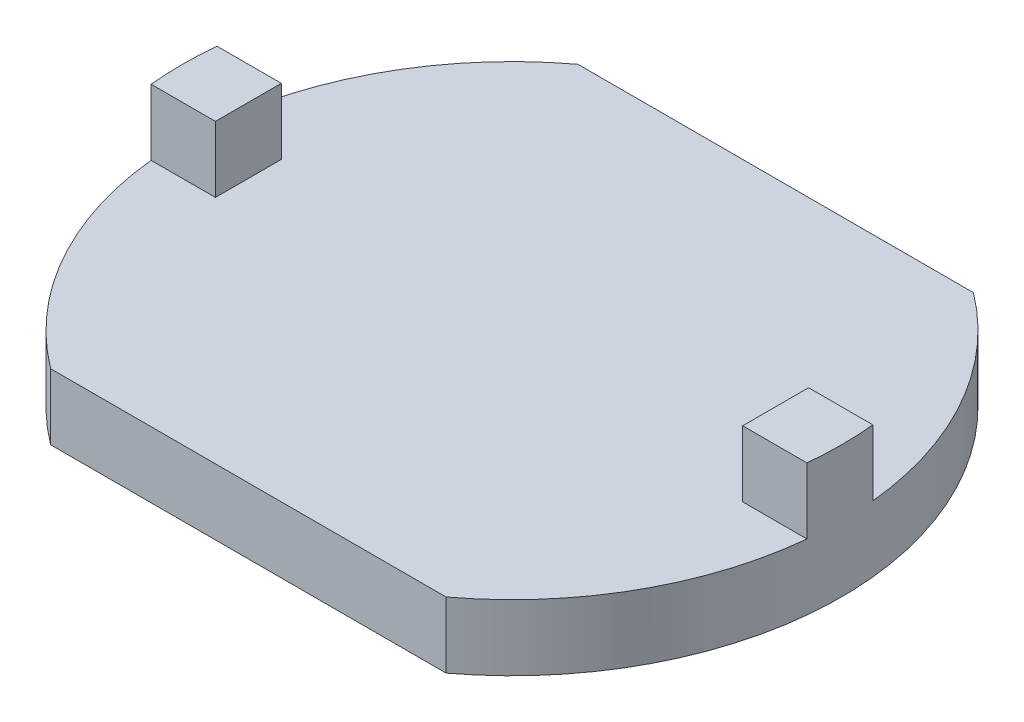
SolidWorks part; units mm, degrees
ref_plane "Front Plane" through (0, 0, 0) normal (0, 0, 1) x (1, 0, 0)
ref_plane "Top Plane" through (0, 0, 0) normal (0, 1, 0) x (1, 0, 0)
ref_plane "Right Plane" through (0, 0, 0) normal (1, 0, 0) x (0, 0, -1)
sketch "Sketch1" plane through (0, 0, 0) normal (0, 1, 0) x (1, 0, 0)
  line L0 (-3, 4) -> (3, 4)
  line L1 (-2.1272, 0) -> (4.3012, 0) construction
  line L2 (-3, -4) -> (3, -4)
  arc A0 (-3, 4) -> (-3, -4) centre (0, 0) ccw
  arc A1 (3, -4) -> (3, 4) centre (0, 0) ccw
  dimension "D1" = 10
  dimension "D2" = 4
extrude "Boss-Extrude1" add sketch "Sketch1" along normal blind 1 contours A0 L2 A1 L0
sketch "Sketch2" plane through (0, 1, 0) normal (0, 1, 0) x (1, 0, 0)
  line L0 (-1.3705, 0) -> (4.9727, 0) construction
  line L1 (0, 1.7654) -> (0, -2.0379) construction
  line L2 (4, -0.5) -> (4.9749, -0.5)
  line L3 (4, -0.5) -> (4, 0.5)
  line L4 (4, 0.5) -> (4.9749, 0.5)
  line L6 (4, -0.5) -> (5, 0.5) construction
  line L7 (4, 0.5) -> (5, -0.5) construction
  line L8 (-4, 0.5) -> (-5, -0.5) construction
  line L9 (-4, -0.5) -> (-5, 0.5) construction
  line L11 (-4, 0.5) -> (-4.9749, 0.5)
  line L12 (-4, -0.5) -> (-4, 0.5)
  line L13 (-4, -0.5) -> (-4.9749, -0.5)
  arc A0 (3, -4) -> (3, 4) centre (0, 0) ccw construction
  arc A1 (4.9749, -0.5) -> (4.9749, 0.5) centre (0, 0) ccw
  arc A2 (-4.9749, 0.5) -> (-4.9749, -0.5) centre (0, 0) ccw
  arc A3 (-3, 4) -> (-3, -4) centre (0, 0) ccw construction
  point P3 (4.5, 0)
  point P17 (-4.5, 0)
  arc M10 (3, -4) -> (3, 4) centre (0, 0) ccw
  dimension "D1" = 1
  dimension "D2" = 1
extrude "Boss-Extrude2" add sketch "Sketch2" along normal blind 1 contours L4 L3 L2 M10 | L12 L11 A2 L13
